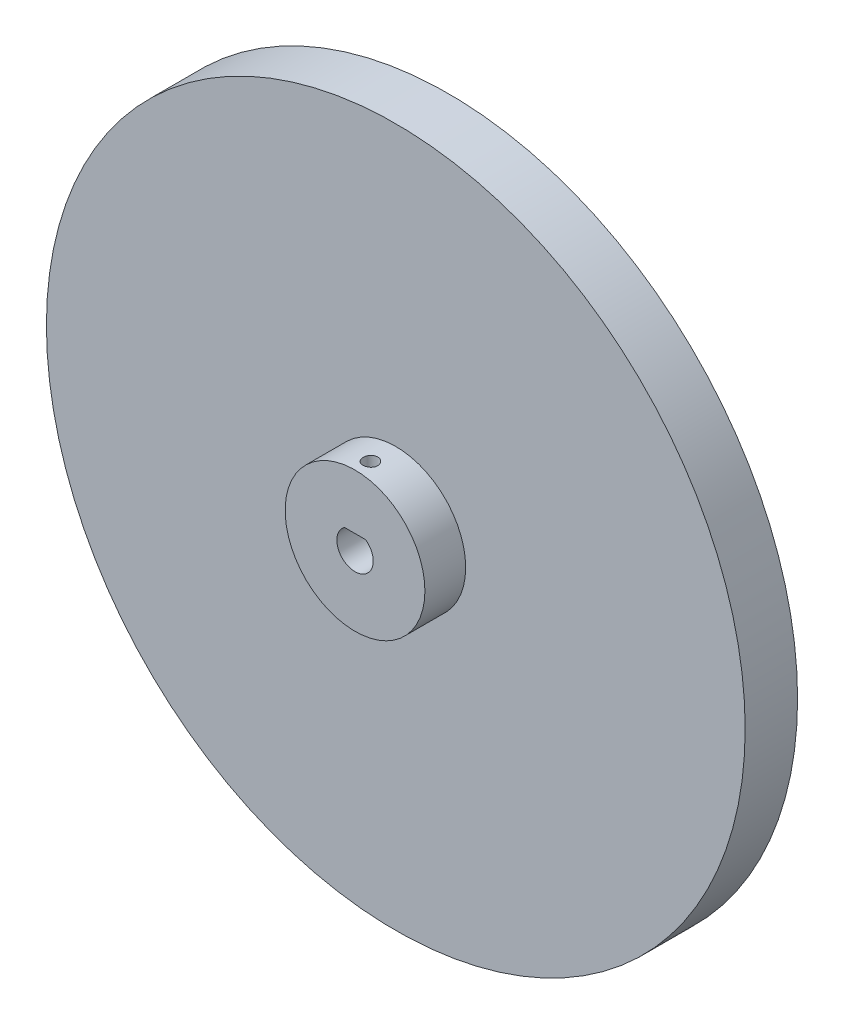
SolidWorks part; units mm, degrees
ref_plane "Plano frontal" through (0, 0, 0) normal (0, 0, 1) x (1, 0, 0)
ref_plane "Plano superior" through (0, 0, 0) normal (0, 1, 0) x (1, 0, 0)
ref_plane "Plano direito" through (0, 0, 0) normal (1, 0, 0) x (0, 0, -1)
sketch "Esboço1" plane through (0, 0, 0) normal (0, 0, 1) x (1, 0, 0)
  line L0 (-1.8064, 2.55) -> (1.8064, 2.55)
  circle A0 centre (0, 0) radius 60
  arc A1 (-1.8064, 2.55) -> (1.8064, 2.55) centre (0, 0) ccw
  dimension "D1" = 120
  dimension "D2" = 6.25
  dimension "D3" = 2.55
extrude "Ressalto-extrusão1" add sketch "Esboço1" along normal blind 9
sketch "Esboço3" plane through (0, 0, 9) normal (0, 0, 1) x (1, 0, 0)
  line L0 (-1.8064, 2.55) -> (1.8064, 2.55)
  circle A0 centre (0, 0) radius 12
  arc A1 (-1.8064, 2.55) -> (1.8064, 2.55) centre (0, 0) ccw
  dimension "D1" = 24
extrude "Ressalto-extrusão2" add sketch "Esboço3" along normal blind 7
sketch "Esboço4" plane through (0, 2.55, 0) normal (0, -1, 0) x (1, 0, 0)
  circle A0 centre (0, 13.3638) radius 1.25
  dimension "D1" = 2.5
extrude "Corte-extrusão1" cut sketch "Esboço4" against normal blind 10
